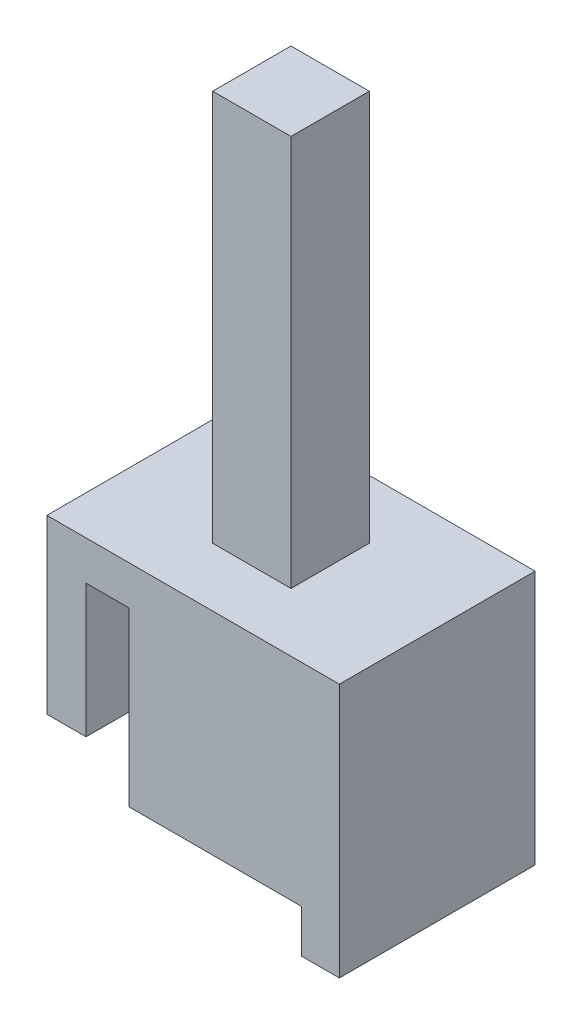
SolidWorks part; units mm, degrees
ref_plane "Front Plane" through (0, 0, 0) normal (0, 0, 1) x (1, 0, 0)
ref_plane "Top Plane" through (0, 0, 0) normal (0, 1, 0) x (1, 0, 0)
ref_plane "Right Plane" through (0, 0, 0) normal (1, 0, 0) x (0, 0, -1)
sketch "Sketch1" plane through (0, 0, 0) normal (0, 0, 1) x (1, 0, 0)
  line L0 (0, 11.176) -> (0, 0)
  line L1 (0, 0) -> (11.176, 0)
  line L2 (11.176, 0) -> (11.176, -2.794)
  line L3 (11.176, -2.794) -> (13.6413, -2.794)
  line L4 (13.6413, -2.794) -> (13.6413, 13.716)
  line L5 (13.6413, 13.716) -> (-5.334, 13.716)
  line L6 (-5.334, 13.716) -> (-5.334, 2.54)
  line L7 (-5.334, 2.54) -> (-2.794, 2.54)
  line L8 (-2.794, 2.54) -> (-2.794, 11.176)
  line L9 (-2.794, 11.176) -> (0, 11.176)
  dimension "D1" = 2.794
  dimension "D2" = 16.4353
  dimension "D3" = 13.97
  dimension "D4" = 13.97
  dimension "D5" = 2.54
  dimension "D6" = 2.54
  dimension "D7" = 2.54
extrude "Boss-Extrude2" add sketch "Sketch1" along normal blind 12.7
sketch "Sketch2" plane through (0, 13.716, 0) normal (0, 1, 0) x (1, 0, 0)
  line L0 (13.6413, 0) -> (-5.334, 0) construction
  line L1 (6.6936, -8.89) -> (1.6136, -8.89)
  line L2 (6.6936, -8.89) -> (6.6936, -3.81)
  line L3 (6.6936, -3.81) -> (1.6136, -3.81)
  line L4 (1.6136, -8.89) -> (1.6136, -3.81)
  line L5 (6.6936, -8.89) -> (1.6136, -3.81) construction
  line L6 (6.6936, -3.81) -> (1.6136, -8.89) construction
  line L7 (-5.334, -12.7) -> (-5.334, 0) construction
  line L8 (-5.334, -6.35) -> (13.6413, -6.35) construction
  line L9 (13.6413, -12.7) -> (13.6413, 0) construction
  point P0 (4.1536, -6.35)
  point P7 (4.1536, 0)
  point P8 (0, 0)
  point P11 (-5.334, -6.35)
  dimension "D1" = 5.08
extrude "Boss-Extrude3" add sketch "Sketch2" along normal blind 25.4
